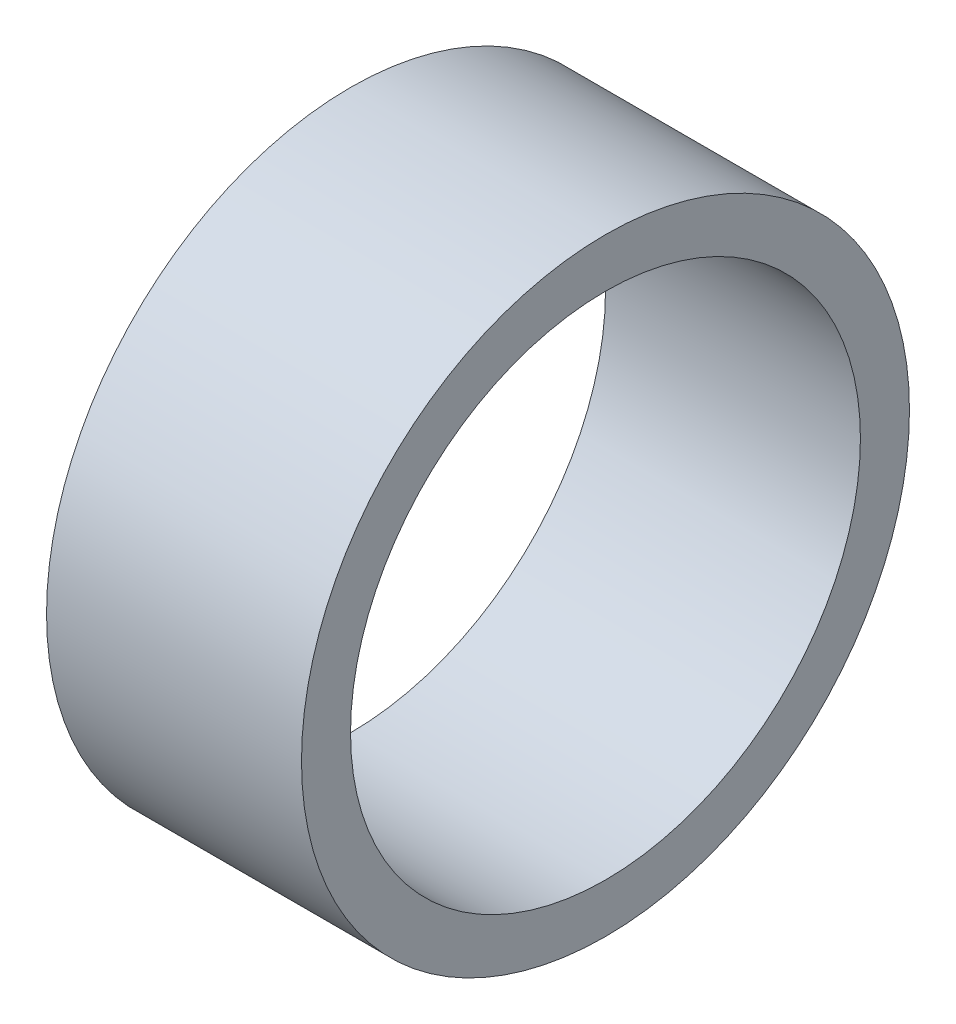
SolidWorks part; units mm, degrees
ref_plane "Front" through (0, 0, 0) normal (0, 0, 1) x (1, 0, 0)
ref_plane "Top" through (0, 0, 0) normal (0, 1, 0) x (1, 0, 0)
ref_plane "Right" through (0, 0, 0) normal (1, 0, 0) x (0, 0, -1)
sketch "Sketch1" plane through (0, 0, 0) normal (1, 0, 0) x (0, 0, -1)
  circle A0 centre (0, 0) radius 26
  circle A1 centre (0, 0) radius 31
  dimension "D1" = 52
  dimension "D2" = 5
extrude "Boss-Extrude1" add sketch "Sketch1" along normal blind 26
